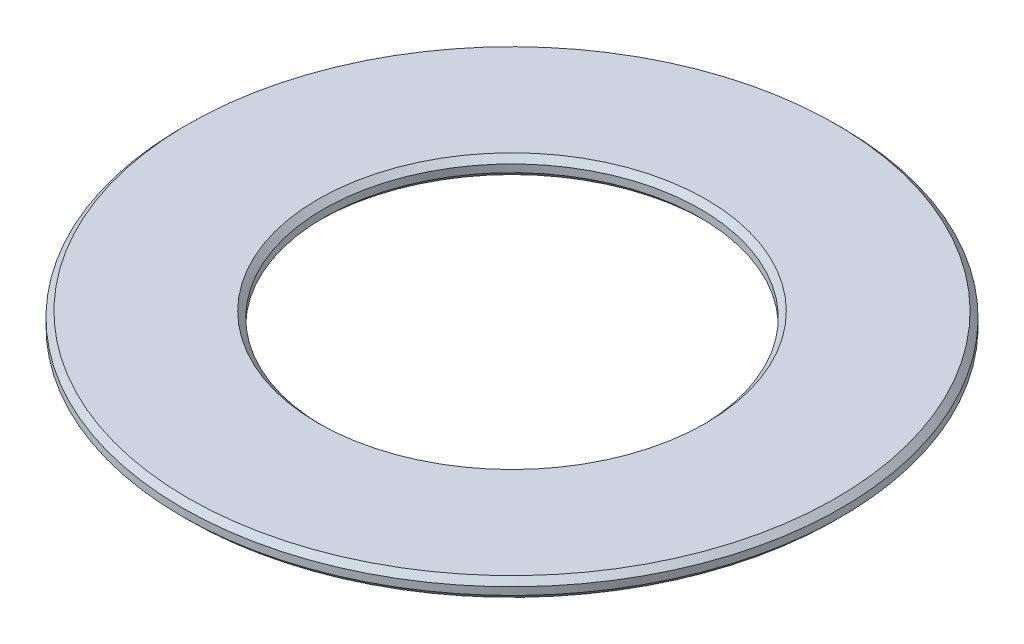
SolidWorks part; units mm, degrees
ref_plane "Front Plane" through (0, 0, 0) normal (0, 0, 1) x (1, 0, 0)
ref_plane "Top Plane" through (0, 0, 0) normal (0, 1, 0) x (1, 0, 0)
ref_plane "Right Plane" through (0, 0, 0) normal (1, 0, 0) x (0, 0, -1)
sketch "Sketch1" plane through (0, 0, 0) normal (0, 1, 0) x (1, 0, 0)
  circle A0 centre (0, 0) radius 17.5
  circle A1 centre (0, 0) radius 10
  dimension "D1" = 20
  dimension "D2" = 35
extrude "Boss-Extrude1" add sketch "Sketch1" along normal mid plane 1
chamfer "Chamfer1" distance 0.3 angle 45 4 edges at (0, -0.5, 17.5) (0, 0.5, 17.5) (0, -0.5, 10) (0, 0.5, 10)
